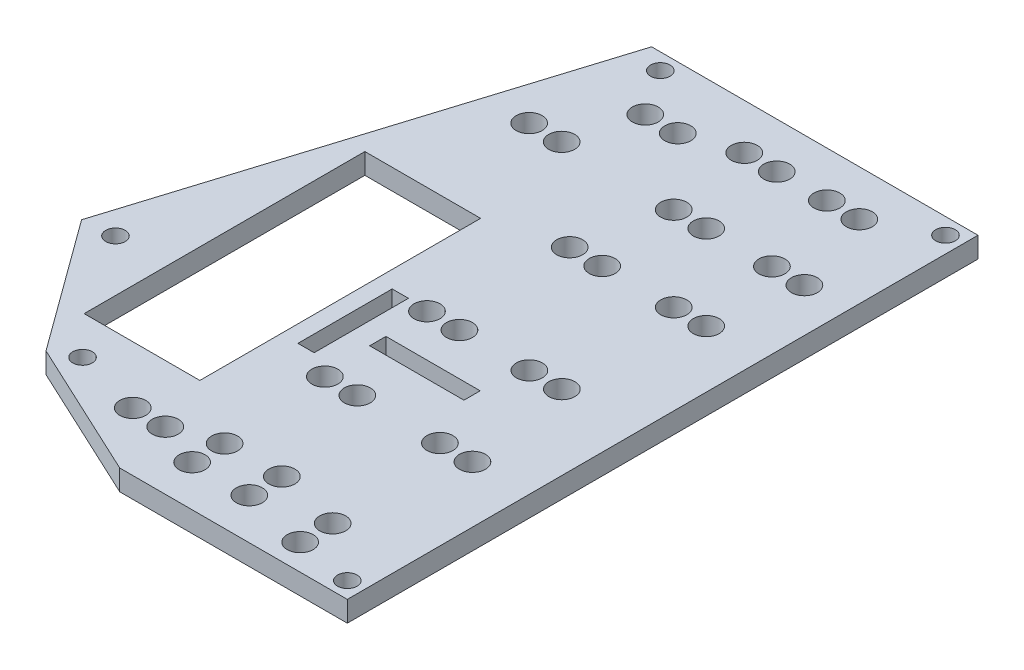
SolidWorks part; units mm, degrees
ref_plane "Front Plane" through (0, 0, 0) normal (0, 0, 1) x (1, 0, 0)
ref_plane "Top Plane" through (0, 0, 0) normal (0, 1, 0) x (1, 0, 0)
ref_plane "Right Plane" through (0, 0, 0) normal (1, 0, 0) x (0, 0, -1)
sketch "Sketch1" plane through (0, 0, 0) normal (0, 1, 0) x (1, 0, 0)
  line L0 (-22.0476, 28.7248) -> (28.1524, 28.7248)
  line L1 (28.1524, 28.7248) -> (28.1524, -68.2788)
  line L2 (28.1524, -68.2788) -> (-6.8476, -68.2788)
  line L5 (28.1524, -68.2788) -> (28.1524, -38.2788) construction
  line L6 (-28.1194, -58.349) -> (-6.8476, -68.2788)
  line L7 (-22.0476, 28.7248) -> (-42.8475, -38.1479)
  line L8 (-42.8475, -38.1479) -> (-28.1194, -58.349)
  line L9 (-7.2476, -23.4752) -> (-9.7476, -23.4752)
  line L18 (-9.7476, -23.4752) -> (-9.7476, -37.9752)
  line L46 (23.2024, -38.2788) -> (28.1524, -38.2788) construction
  line L51 (-2.0476, -61.9488) -> (-8.7476, -61.9488) construction
  line L55 (-9.7476, -37.9752) -> (-7.2476, -37.9752)
  line L56 (-7.2476, -37.9752) -> (-7.2476, -23.4752)
  line L57 (10.5924, -30.2788) -> (10.5924, -32.7788)
  line L58 (-3.9076, -30.2788) -> (-3.9076, -32.7788)
  line L59 (-3.9076, -30.2788) -> (10.5924, -30.2788)
  line L60 (-3.9076, -32.7788) -> (10.5924, -32.7788)
  line L62 (-30.1476, -7.2752) -> (-12.3476, -7.2752)
  line L63 (-30.1476, -7.2752) -> (-30.1476, -50.4552)
  line L64 (-30.1476, -50.4552) -> (-12.3476, -50.4552)
  line L65 (-12.3476, -7.2752) -> (-12.3476, -50.4552)
  circle A4 centre (25.6524, 26.2248) radius 1.5
  circle A5 centre (25.6524, -65.7788) radius 1.5
  circle A7 centre (-38.0871, -37.6942) radius 1.5
  circle A8 centre (-18.207, 26.2212) radius 1.5
  circle A9 centre (-24.4482, -56.4013) radius 1.5
  circle A10 centre (16.9024, 21.7248) radius 2
  circle A11 centre (11.9024, 21.7248) radius 2
  circle A12 centre (4.2024, 21.7248) radius 2
  circle A13 centre (-0.7976, 21.7248) radius 2
  circle A14 centre (-8.5181, 19.2212) radius 2
  circle A15 centre (-13.5181, 19.2212) radius 2
  circle A16 centre (-16.3015, 9.1469) radius 2
  circle A17 centre (-21.3015, 9.1469) radius 2
  circle A18 centre (-2.0476, -61.9488) radius 2
  circle A19 centre (-2.0476, -56.9488) radius 2
  circle A20 centre (6.7524, -61.9488) radius 2
  circle A21 centre (6.7524, -56.9488) radius 2
  circle A22 centre (-8.8476, -59.2788) radius 2
  circle A23 centre (-13.8476, -59.2788) radius 2
  circle A24 centre (21.4524, 8.7248) radius 2
  circle A25 centre (16.4524, 8.7248) radius 2
  circle A26 centre (6.3524, 8.7248) radius 2
  circle A27 centre (1.3524, 8.7248) radius 2
  circle A28 centre (14.3524, -4.2752) radius 2
  circle A29 centre (19.3524, -4.2752) radius 2
  circle A30 centre (3.3524, -4.2752) radius 2
  circle A31 centre (-1.6476, -4.2752) radius 2
  circle A32 centre (16.6524, -23.7788) radius 2
  circle A33 centre (11.6524, -23.7788) radius 2
  circle A34 centre (0.9024, -23.7788) radius 2
  circle A35 centre (-4.0976, -23.7788) radius 2
  circle A36 centre (19.4524, -40.334) radius 2
  circle A37 centre (14.4524, -40.334) radius 2
  circle A38 centre (1.7524, -40.334) radius 2
  circle A39 centre (-3.2476, -40.334) radius 2
  circle A40 centre (16.9024, -59.2788) radius 2
  circle A41 centre (16.9024, -64.2788) radius 2
  dimension "D37" = 3
  dimension "D39" = 2.5
  dimension "D40" = 3
  dimension "D41" = 2.5
  dimension "D42" = 2.5
  dimension "D43" = 4
  dimension "D44" = 6.33
  dimension "D45" = 5
  dimension "D46" = 3
  dimension "D47" = 4
  dimension "D48" = 20
  dimension "D49" = 3
  dimension "D50" = 20
  dimension "D51" = 4
  dimension "D8" = 3
  dimension "D9" = 9.5037
  dimension "D13" = 4
  dimension "D15" = 4
  dimension "D19" = 4
  dimension "D21" = 4
  dimension "D26" = 4
  dimension "D28" = 4
  dimension "D29" = 4
  dimension "D30" = 4
  dimension "D32" = 17.56
  dimension "D52" = 4
  dimension "D53" = 4
  dimension "D56" = 4
  dimension "D58" = 4
  dimension "D60" = 4
  dimension "D36" = 21.4
  dimension "D23" = 4
  dimension "D66" = 4
  dimension "D70" = 4
  dimension "D74" = 4
  dimension "D75" = 4
  dimension "D78" = 4
  dimension "D81" = 4
  dimension "D84" = 4
  dimension "D90" = 8.7
  dimension "D4" = 30
  dimension "D5" = 71
  dimension "D6" = 25
  dimension "D7" = 35
  dimension "D10" = 6.7
  dimension "D11" = 11.25
  dimension "D12" = 7
  dimension "D14" = 5
  dimension "D16" = 7
  dimension "D17" = 7.7
  dimension "D18" = 7
  dimension "D20" = 5
  dimension "D22" = 7
  dimension "D24" = 5
  dimension "D25" = 5
  dimension "D27" = 4.95
  dimension "D31" = 5
  dimension "D33" = 35.5
  dimension "D34" = 35.4
  dimension "D35" = 52.2
  dimension "D38" = 2.5
  dimension "D54" = 6.33
  dimension "D55" = 8.8
  dimension "D57" = 8.8
  dimension "D59" = 9
  dimension "D61" = 5
  dimension "D62" = 21.4
  dimension "D63" = 37
  dimension "D64" = 10.1
  dimension "D65" = 20
  dimension "D67" = 5
  dimension "D68" = 20
  dimension "D69" = 8.8
  dimension "D71" = 33
  dimension "D72" = 33
  dimension "D73" = 5
  dimension "D76" = 11
  dimension "D77" = 33
  dimension "D79" = 5
  dimension "D80" = 33
  dimension "D82" = 11.5
  dimension "D83" = 44.5
  dimension "D85" = 5
  dimension "D86" = 44.5
  dimension "D87" = 5
  dimension "D88" = 44.5
  dimension "D89" = 10.75
  dimension "D91" = 5
  dimension "D92" = 12.7
  dimension "D93" = 5
  dimension "D94" = 5
  dimension "D95" = 4
  dimension "D96" = 11.25
  dimension "D97" = 43.18
  dimension "D98" = 17.8
  dimension "D99" = 40.5
  dimension "D100" = 36
extrude "Boss-Extrude1" add sketch "Sketch1" along normal blind 3.175
